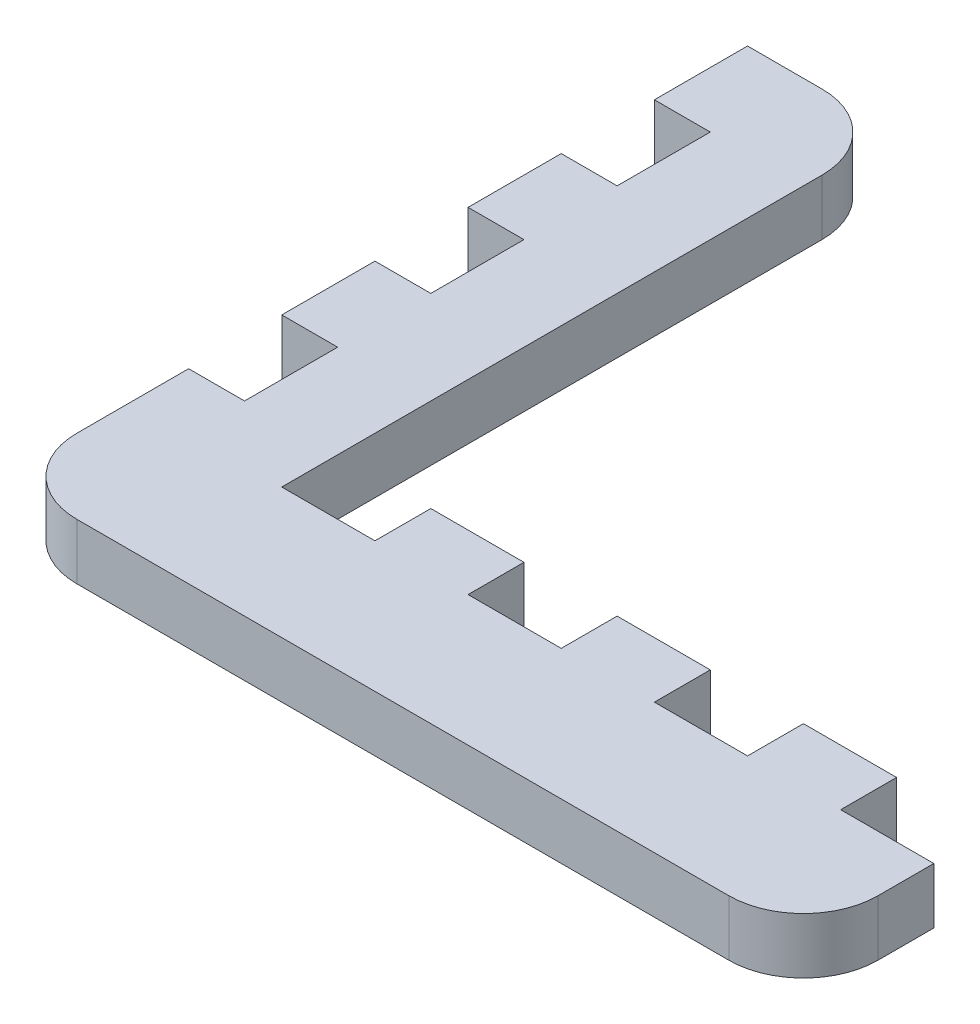
SolidWorks part; units mm, degrees
ref_plane "Front Plane" through (0, 0, 0) normal (0, 0, 1) x (1, 0, 0)
ref_plane "Top Plane" through (0, 0, 0) normal (0, 1, 0) x (1, 0, 0)
ref_plane "Right Plane" through (0, 0, 0) normal (1, 0, 0) x (0, 0, -1)
sketch "Sketch1" plane through (0, 0, 0) normal (0, 1, 0) x (1, 0, 0)
  line L1 (-23, 20) -> (23, 20)
  line L2 (-23, 20) -> (-23, -20)
  line L3 (-23, -20) -> (23, -20)
  line L4 (23, 20) -> (23, -20)
  line L5 (-23, 20) -> (23, -20) construction
  line L6 (-23, -20) -> (23, 20) construction
  point P0 (0, 0)
  dimension "D1" = 40
  dimension "D2" = 46
extrude "Boss-Extrude1" add sketch "Sketch1" along normal blind 3
sketch "Sketch3" plane through (0, 3, 0) normal (0, 1, 0) x (1, 0, 0)
  line L1 (23, 20) -> (-12, 20)
  line L2 (23, 20) -> (23, -10)
  line L3 (23, -10) -> (-12, -10)
  line L4 (-12, 20) -> (-12, -10)
  dimension "D1" = 35
  dimension "D2" = 30
extrude "Cut-Extrude1" cut sketch "Sketch3" against normal up to surface (3 mm away) up to face at (0, 0, 0)
sketch "Sketch4" plane through (0, 0, 10) normal (0, 0, -1) x (-1, 0, 0)
  line L0 (-23, 0) -> (12, 0) construction
  line L1 (-23, 3) -> (-18, 3)
  line L2 (-23, 3) -> (-23, 0)
  line L3 (-23, 0) -> (-18, 0)
  line L4 (-18, 3) -> (-18, 0)
  line L5 (12, 3) -> (-23, 3) construction
  line L6 (-18, 0) -> (-13, 0)
  line L7 (-18, 0) -> (-18, 3)
  line L8 (-18, 3) -> (-13, 3)
  line L9 (-13, 0) -> (-13, 3)
  line L11 (-13, 3) -> (-8, 3)
  line L12 (-13, 3) -> (-13, 0)
  line L13 (-13, 0) -> (-8, 0)
  line L14 (-8, 3) -> (-8, 0)
  line L15 (-8, 0) -> (-3, 0)
  line L16 (-8, 0) -> (-8, 3)
  line L17 (-8, 3) -> (-3, 3)
  line L18 (-3, 0) -> (-3, 3)
  line L19 (-3, 3) -> (2, 3)
  line L20 (-3, 3) -> (-3, 0)
  line L21 (-3, 0) -> (2, 0)
  line L22 (2, 3) -> (2, 0)
  line L23 (2, 0) -> (7, 0)
  line L24 (2, 0) -> (2, 3)
  line L25 (2, 3) -> (7, 3)
  line L26 (7, 0) -> (7, 3)
  line M16 (-23, 0) -> (12, 0)
  line M18 (12, 3) -> (-23, 3)
  dimension "D1" = 5
extrude "Cut-Extrude3" cut sketch "Sketch4" against normal blind 3 contours L9 L4 M16 M18 | L18 L14 M16 M18 | L26 L22 M16 M18
sketch "Sketch6" plane through (23, 0, 0) normal (1, 0, 0) x (0, 0, -1)
  line L0 (-20, 0) -> (-10, 0) construction
  line L1 (-20, 3) -> (-13, 3)
  line L2 (-20, 3) -> (-20, 0)
  line L3 (-20, 0) -> (-13, 0)
  line L4 (-13, 3) -> (-13, 0)
  line L5 (-13, 0) -> (-13, 3) construction
extrude "Boss-Extrude2" add sketch "Sketch6" along normal blind 5
sketch "Sketch7" plane through (0, 0, 0) normal (0, -1, 0) x (1, 0, 0)
  line L0 (-23, 20) -> (28, 20) construction
  line L1 (-23, -20) -> (-12, -20)
  line L2 (-23, -20) -> (-23, 20)
  line L3 (-23, 20) -> (-12, 20)
  line L4 (-12, -20) -> (-12, 20)
  line L5 (-12, 10) -> (-12, -20) construction
extrude "Cut-Extrude4" cut sketch "Sketch7" against normal up to surface (3 mm away) up to face at (4.9, 3, 9.2)
sketch "Sketch8" plane through (0, 0, 10) normal (0, 0, -1) x (-1, 0, 0)
  line L1 (7, 3) -> (12, 3)
  line L2 (7, 3) -> (7, 0)
  line L3 (7, 0) -> (12, 0)
  line L4 (12, 3) -> (12, 0)
extrude "Boss-Extrude3" add sketch "Sketch8" along normal blind 30
sketch "Sketch9" plane through (-12, 0, 0) normal (-1, 0, 0) x (0, 0, 1)
  line L0 (-20, 3) -> (20, 3) construction
  line L1 (-20, 0) -> (-15, 0)
  line L2 (-20, 0) -> (-20, 3)
  line L3 (-20, 3) -> (-15, 3)
  line L4 (-15, 0) -> (-15, 3)
  line L5 (-20, 0) -> (20, 0) construction
  line L6 (-15, 3) -> (-10, 3)
  line L7 (-15, 3) -> (-15, 0)
  line L8 (-15, 0) -> (-10, 0)
  line L9 (-10, 3) -> (-10, 0)
  line L11 (-10, 0) -> (-5, 0)
  line L12 (-10, 0) -> (-10, 3)
  line L13 (-10, 3) -> (-5, 3)
  line L14 (-5, 0) -> (-5, 3)
  line L15 (-5, 3) -> (0, 3)
  line L16 (-5, 3) -> (-5, 0)
  line L17 (-5, 0) -> (0, 0)
  line L18 (0, 3) -> (0, 0)
  line L19 (0, 0) -> (5, 0)
  line L20 (0, 0) -> (0, 3)
  line L21 (0, 3) -> (5, 3)
  line L22 (5, 0) -> (5, 3)
  line L23 (20, 0) -> (10, 0)
  line L24 (20, 0) -> (20, 3)
  line L25 (20, 3) -> (10, 3)
  line L26 (10, 0) -> (10, 3)
  line M9 (-20, 0) -> (20, 0)
  line M11 (20, 3) -> (-20, 3)
  line M12 (-20, 3) -> (-20, 0)
  dimension "D1" = 5
  dimension "D2" = 10
extrude "Boss-Extrude4" add sketch "Sketch9" along normal blind 3 contours L4 M9 M11 M12 | L14 L9 M9 M11 | L22 L18 M9 M11 | L24 L23 L26 L25
fillet "Fillet2" radius 4 3 edges at (-15, 1.5, 20) (-7, 1.5, -20) (28, 1.5, 20)
